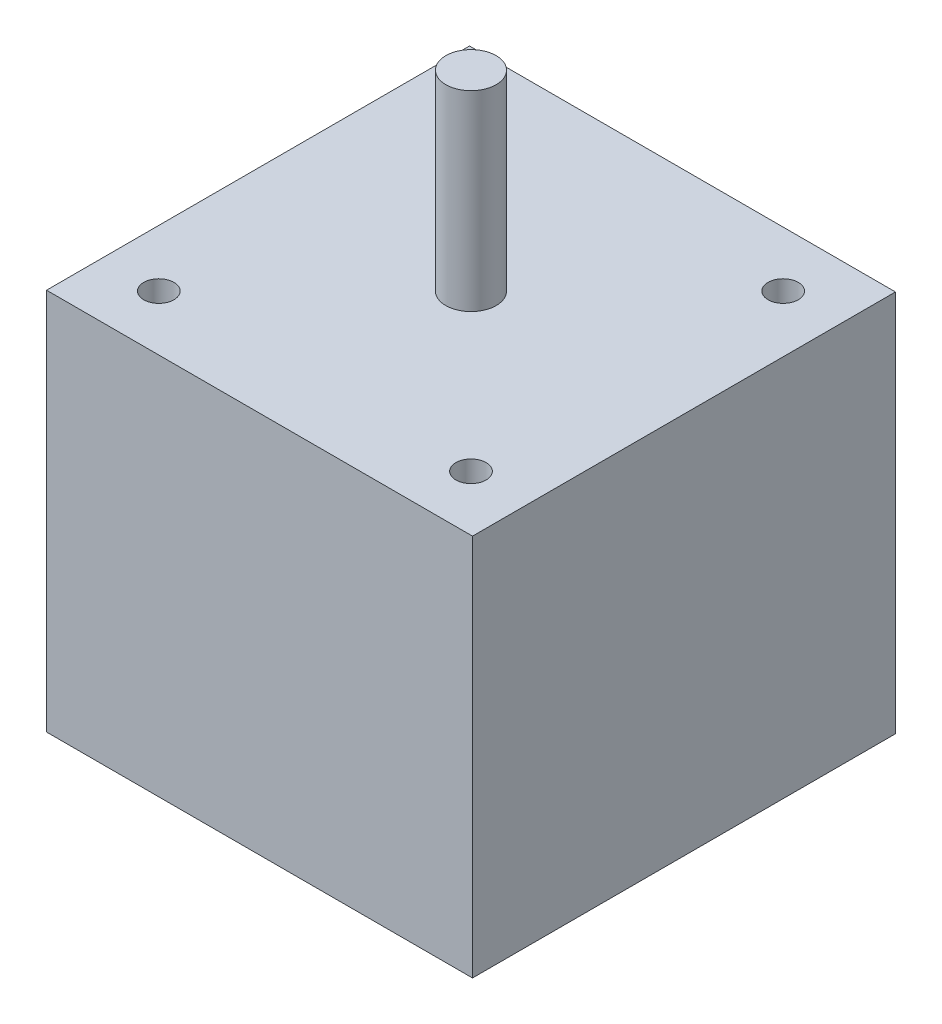
SolidWorks part; units mm, degrees
ref_plane "Front Plane" through (0, 0, 0) normal (0, 0, 1) x (1, 0, 0)
ref_plane "Top Plane" through (0, 0, 0) normal (0, 1, 0) x (1, 0, 0)
ref_plane "Right Plane" through (0, 0, 0) normal (1, 0, 0) x (0, 0, -1)
sketch "Sketch1" plane through (0, 0, 0) normal (0, 1, 0) x (1, 0, 0)
  line L1 (-21.15, -21) -> (21.15, -21)
  line L2 (-21.15, -21) -> (-21.15, 21)
  line L3 (-21.15, 21) -> (21.15, 21)
  line L4 (21.15, -21) -> (21.15, 21)
  line L5 (-21.15, -21) -> (21.15, 21) construction
  line L6 (-21.15, 21) -> (21.15, -21) construction
  point P0 (0, 0)
  dimension "D1" = 42.3
  dimension "D2" = 42
extrude "Boss-Extrude1" add sketch "Sketch1" along normal blind 38
sketch "Sketch2" plane through (0, 38, 0) normal (0, 1, 0) x (1, 0, 0)
  circle A0 centre (0, 0) radius 2.5
  dimension "D1" = 5
extrude "Boss-Extrude2" add sketch "Sketch2" along normal blind 19
sketch "Sketch3" plane through (0, 38, 0) normal (0, 1, 0) x (1, 0, 0)
  line L0 (-15.5, 15.5) -> (15.5, 15.5) construction
  line L1 (15.5, 15.5) -> (15.5, -15.5) construction
  line L2 (15.5, -15.5) -> (-15.5, -15.5) construction
  line L3 (-15.5, -15.5) -> (-15.5, 15.5) construction
  circle A0 centre (-15.5, 15.5) radius 1.5
  circle A1 centre (15.5, 15.5) radius 1.5
  circle A2 centre (15.5, -15.5) radius 1.5
  circle A3 centre (-15.5, -15.5) radius 1.5
  point P8 (0, 15.5)
  point P11 (-15.5, 0)
  dimension "D1" = 3
  dimension "D2" = 31
  dimension "D3" = 31
extrude "Cut-Extrude1" cut sketch "Sketch3" against normal blind 4.5
